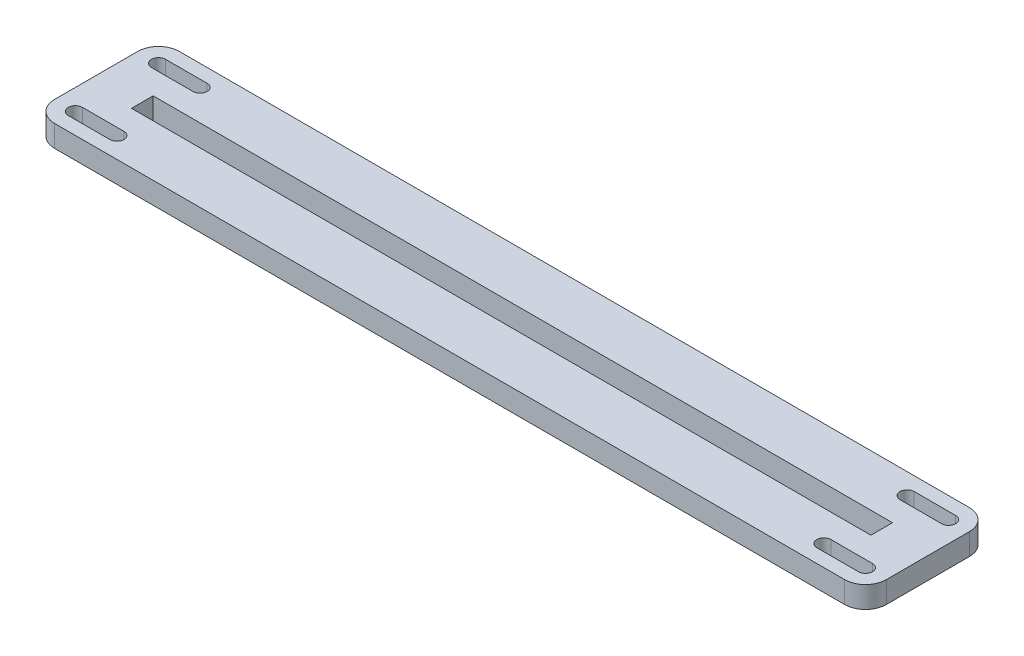
SolidWorks part; units mm, degrees
material "Acrylic (BLUE)"
ref_plane "Front Plane" through (0, 0, 0) normal (0, 0, 1) x (1, 0, 0)
ref_plane "Top Plane" through (0, 0, 0) normal (0, 1, 0) x (1, 0, 0)
ref_plane "Right Plane" through (0, 0, 0) normal (1, 0, 0) x (0, 0, -1)
sketch "Sketch1" plane through (0, 0, 0) normal (0, 1, 0) x (1, 0, 0)
  line L0 (-127, 19.05) -> (127, -19.05) construction
  line L1 (-127, 19.05) -> (127, 19.05)
  line L2 (-127, 19.05) -> (-127, -19.05)
  line L3 (-127, -19.05) -> (127, -19.05)
  line L4 (127, 19.05) -> (127, -19.05)
  line L5 (-112.903, 3.302) -> (112.903, -3.302) construction
  line L6 (-112.903, 3.302) -> (112.903, 3.302)
  line L7 (-112.903, 3.302) -> (-112.903, -3.302)
  line L8 (-112.903, -3.302) -> (112.903, -3.302)
  line L9 (112.903, 3.302) -> (112.903, -3.302)
  dimension "D1" = 254
  dimension "D2" = 38.1
  dimension "D3" = 225.806
  dimension "D4" = 6.604
extrude "Boss-Extrude1" add sketch "Sketch1" along normal blind 6.604
sketch "Sketch2" plane through (0, 6.604, 0) normal (0, 1, 0) x (1, 0, 0)
  line L0 (-114.3, 0) -> (-114.3, 12.7) construction
  line L1 (-120.65, 12.7) -> (-107.95, 12.7) construction
  line L2 (-120.65, 14.859) -> (-107.95, 14.859)
  line L3 (-120.65, 10.541) -> (-107.95, 10.541)
  line L4 (-114.3, 0) -> (-114.3, -12.7) construction
  line L5 (-120.65, -12.7) -> (-107.95, -12.7) construction
  line L6 (-120.65, -10.541) -> (-107.95, -10.541)
  line L7 (-120.65, -14.859) -> (-107.95, -14.859)
  line L8 (0, 0) -> (-114.3, 0) construction
  arc A0 (-120.65, 14.859) -> (-120.65, 10.541) centre (-120.65, 12.7) ccw
  arc A1 (-107.95, 10.541) -> (-107.95, 14.859) centre (-107.95, 12.7) ccw
  arc A2 (-120.65, -10.541) -> (-120.65, -14.859) centre (-120.65, -12.7) ccw
  arc A3 (-107.95, -14.859) -> (-107.95, -10.541) centre (-107.95, -12.7) ccw
  point P4 (-114.3, 12.7)
  point P14 (-114.3, -12.7)
  dimension "D1" = 12.7
  dimension "D2" = 4.318
  dimension "D3" = 12.7
  dimension "D4" = 114.3
extrude "Cut-Extrude1" cut sketch "Sketch2" against normal through all
mirror "Mirror1" about plane through (0, 0, 0) normal (1, 0, 0) of "Cut-Extrude1"
fillet "Fillet1" radius 6.35 4 edges at (-127, 3.302, 19.05) (127, 3.302, 19.05) (-127, 3.302, -19.05) (127, 3.302, -19.05)
other "Move Face1" [suppressed] parameters "D1"=0.0508
